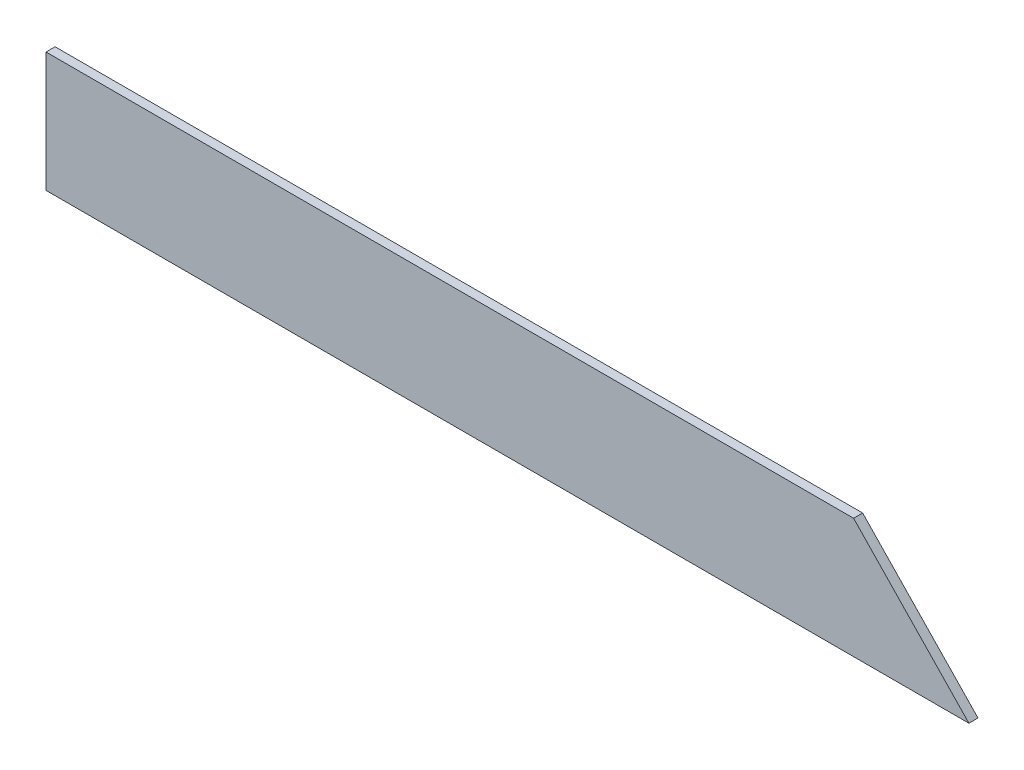
SolidWorks part; units mm, degrees
material "Pine"
ref_plane "Front Plane" through (0, 0, 0) normal (0, 0, 1) x (1, 0, 0)
ref_plane "Top Plane" through (0, 0, 0) normal (0, 1, 0) x (1, 0, 0)
ref_plane "Right Plane" through (0, 0, 0) normal (1, 0, 0) x (0, 0, -1)
sketch "Sketch1" plane through (0, 0, 0) normal (0, 0, 1) x (1, 0, 0)
  line L0 (728.3618, 98.7055) -> (496.2058, 340.0055)
  line L1 (-1129.3942, 340.0055) -> (496.2058, 340.0055)
  line L2 (-1129.3942, 340.0055) -> (-1129.3942, 98.7055)
  line L3 (-1129.3942, 98.7055) -> (728.3618, 98.7055)
  dimension "D1" = 241.3
  dimension "D2" = 1857.756
  dimension "D3" = 1625.6
  dimension "D4" = 46.106
extrude "Boss-Extrude1" add sketch "Sketch1" along normal blind 18.2562
sketch "Sketch3" plane through (-1129.3942, 0, 0) normal (-1, 0, 0) x (0, 0, 1)
  line L4 (-2.0122, 80.8078) -> (0, 157.6519)
  line L5 (0, 340.0055) -> (0, 98.7055) construction
  line L6 (0, 157.6519) -> (18.4486, 80.8078)
  line L7 (18.4486, 80.8078) -> (-2.0122, 80.8078)
  line L8 (18.2562, 98.7055) -> (0, 98.7055) construction
  dimension "D1" = 15
  dimension "D2" = 17.8977
  dimension "D3" = 58.9463
extrude "Cut-Extrude1" [suppressed] cut sketch "Sketch3" against normal through all
chamfer "Chamfer1" [suppressed] distance 63.5 angle 15
